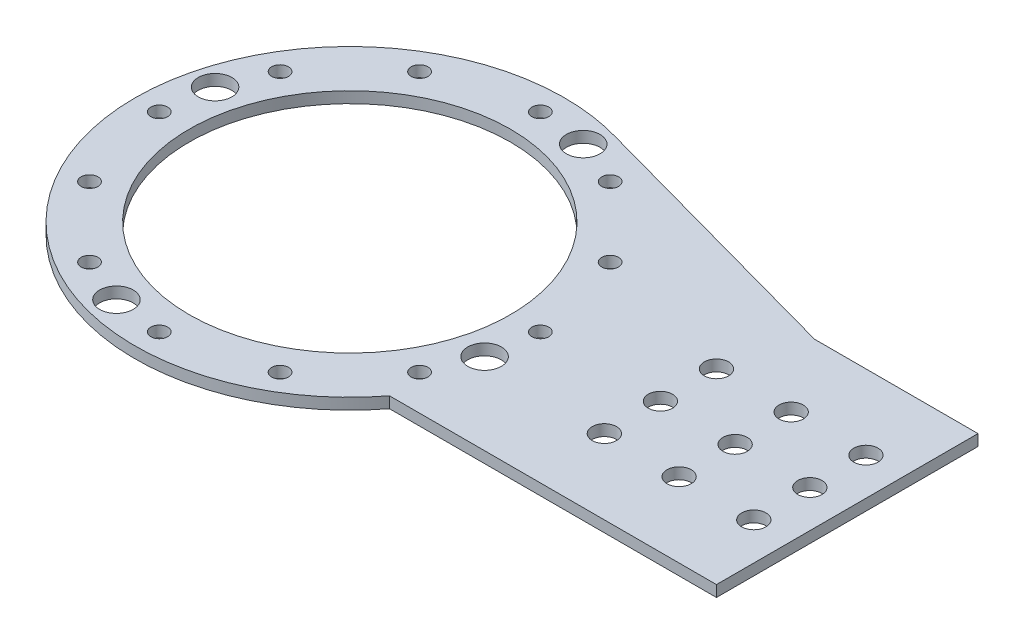
SolidWorks part; units mm, degrees
ref_plane "Front Plane" through (0, 0, 0) normal (0, 0, 1) x (1, 0, 0)
ref_plane "Top Plane" through (0, 0, 0) normal (0, 1, 0) x (1, 0, 0)
ref_plane "Right Plane" through (0, 0, 0) normal (1, 0, 0) x (0, 0, -1)
sketch "Sketch1" plane through (0, 0, 0) normal (0, 1, 0) x (1, 0, 0)
  circle A0 centre (0, 0) radius 57.5
  dimension "D1" = 115
extrude "Boss-Extrude1" add sketch "Sketch1" along normal blind 3
sketch "Sketch2" plane through (0, 0, 0) normal (0, 1, 0) x (1, 0, 0)
  line L0 (133.1258, 35) -> (-6.8742, 35)
  line L1 (133.1258, 35) -> (133.1258, -35)
  line L2 (-6.8742, 35) -> (-6.8742, -35)
  line L3 (133.1258, -35) -> (-6.8742, -35)
  line L4 (-6.8742, 0) -> (133.1258, 0) construction
  line L5 (63.1258, 35) -> (63.1258, -35) construction
  point P1 (63.1258, 0)
  dimension "D1" = 70
  dimension "D2" = 140
extrude "Boss-Extrude2" add sketch "Sketch2" along normal blind 3
sketch "Sketch3" plane through (0, 0, 0) normal (0, 1, 0) x (1, 0, 0)
  line L0 (89.3733, 35) -> (13.7685, 55.8272)
  line L1 (133.1258, 35) -> (45.6207, 35) construction
  line L2 (13.7685, 55.8272) -> (13.7685, 13.5588)
  line L3 (13.7685, 13.5588) -> (89.3733, 35)
  arc A0 (45.6207, 35) -> (45.6207, -35) centre (0, 0) ccw construction
extrude "Boss-Extrude3" add sketch "Sketch3" along normal blind 3
mirror "Mirror1" [suppressed] about plane through (0, 0, 0) normal (0, 0, 1)
sketch "Sketch4" plane through (0, 3, 0) normal (0, 1, 0) x (1, 0, 0)
  circle A0 centre (0, 0) radius 43
  dimension "D1" = 86
extrude "Cut-Extrude1" cut sketch "Sketch4" against normal through all
sketch "Sketch7" plane through (0, 3, 0) normal (0, 1, 0) x (1, 0, 0)
  line L0 (0, 0) -> (133.1258, 0) construction
  line L1 (133.1258, -35) -> (133.1258, 35) construction
  line L2 (123.1258, 15) -> (123.1258, -15) construction
  circle A0 centre (123.1258, 15) radius 3.25
  circle A1 centre (123.1258, -15) radius 3.25
  point P8 (123.1258, 0)
  dimension "D1" = 6.5
  dimension "D2" = 30
  dimension "D3" = 10
extrude "Cut-Extrude8" cut sketch "Sketch7" against normal through all
pattern_linear "LPattern1" count 3 spacing 20 along (-1, 0, 0) of "Cut-Extrude8"
sketch "Sketch5" plane through (0, 0, 0) normal (0, 1, 0) x (1, 0, 0)
  circle A0 centre (0, 0) radius 51 construction
  circle A1 centre (-51, 0) radius 2.25
  dimension "D1" = 4.5
  dimension "D2" = 102
extrude "Cut-Extrude5" cut sketch "Sketch5" against normal through all and the other way through all contours A1
pattern_circular "CirPattern1" count 12 over 360 about axis through (0, 0, 0) along (0, 1, 0) of "Cut-Extrude5"
sketch "Sketch11" plane through (0, 3, 0) normal (0, 1, 0) x (1, 0, 0)
  line L0 (52.9426, -35) -> (62.7348, -25.9656)
  line L1 (45.6207, -35) -> (133.1258, -35) construction
  line L2 (62.7348, -25.9656) -> (71.0702, -35)
  line L3 (71.0702, -35) -> (52.9426, -35)
extrude "Cut-Extrude16" [suppressed] cut sketch "Sketch11" against normal through all
sketch "Sketch12" plane through (0, 3, 0) normal (0, 1, 0) x (1, 0, 0)
  line L0 (0, 0) -> (-51, 0) construction
  line L1 (0, 0) -> (-49.2622, 13.1998) construction
  circle A0 centre (0, 0) radius 51 construction
  circle A1 centre (-49.2622, 13.1998) radius 4.5
  dimension "D1" = 102
  dimension "D2" = 9
  dimension "D3" = 15
extrude "Cut-Extrude17" cut sketch "Sketch12" against normal through all
pattern_circular "CirPattern2" count 4 over 360 about axis through (0, 0, 0) along (0, 1, 0) of "Cut-Extrude17"
sketch "Sketch13" plane through (0, 3, 0) normal (0, 1, 0) x (1, 0, 0)
  line L0 (133.1258, 0) -> (0, 0) construction
  line L1 (133.1258, -35) -> (133.1258, 35) construction
  circle A0 centre (123.1258, 0) radius 3.25
  dimension "D1" = 6.5
  dimension "D2" = 10
extrude "Cut-Extrude18" cut sketch "Sketch13" against normal blind 10 contours A0
pattern_linear "LPattern2" count 3 spacing 20 along (-1, 0, 0) of "Cut-Extrude18"
